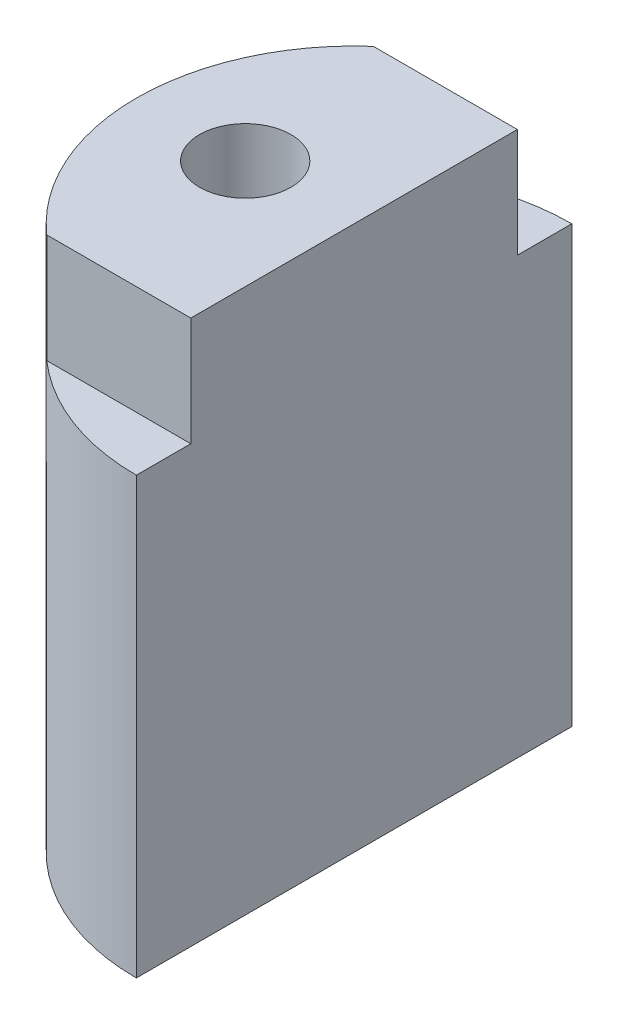
SolidWorks part; units mm, degrees
material "Brass"
ref_plane "Front Plane" through (0, 0, 0) normal (0, 0, 1) x (1, 0, 0)
ref_plane "Top Plane" through (0, 0, 0) normal (0, 1, 0) x (1, 0, 0)
ref_plane "Right Plane" through (0, 0, 0) normal (1, 0, 0) x (0, 0, -1)
sketch "Sketch1" plane through (0, 0, 0) normal (0, 1, 0) x (1, 0, 0)
  line L0 (0, 10) -> (0, -10)
  arc A4 (0, 10) -> (0, -10) centre (0, 0) ccw
  dimension "D1" = 20
extrude "Boss-Extrude1" add sketch "Sketch1" along normal blind 25
sketch "Sketch4" plane through (0, 25, 0) normal (0, 1, 0) x (1, 0, 0)
  circle A0 centre (0, 0) radius 3
  dimension "D1" = 6
sketch "Sketch18" plane through (0, 25, 0) normal (0, 1, 0) x (1, 0, 0)
  line L0 (0, 10) -> (0, -10)
  line L1 (0, 7.5) -> (-6.6144, 7.5)
  line L2 (0, -7.5) -> (-6.6144, -7.5)
  arc A1 (0, 10) -> (0, -10) centre (0, 0) ccw
  arc M6 (0, 10) -> (0, -10) centre (0, 0) ccw
  line M8 (0, -10) -> (0, 10)
  dimension "D1" = 7.5
  dimension "D2" = 20
  dimension "D3" = 7.5
extrude "Cut-Extrude1" cut sketch "Sketch18" against normal blind 5 contours L1 L0 M6 | L2 M8 M6
sketch "Sketch19" plane through (0, 25, 0) normal (0, 1, 0) x (1, 0, 0)
  line L0 (0, 0) -> (-10, 0) construction
  arc A0 (-6.6144, 7.5) -> (-6.6144, -7.5) centre (0, 0) ccw construction
hole_wizard "M5 Tapped Hole1" positions "Sketch20" profile "Sketch21" tap size "M5" standard "ISO"
sketch "Sketch20" plane through (0, 25, 0) normal (0, 1, 0) x (1, 0, 0)
  line L0 (0, 0) -> (-10, 0) construction
  point P0 (-5, 0)
sketch "Sketch21" plane through (-5, 25, 0) normal (1, 0, 0) x (0, 0, 1)
  line L0 (0, 0) -> (0, 12.4)
  line L1 (0, 12.4) -> (2.1, 11.1382)
  line L2 (2.1, 11.1382) -> (2.1, 0)
  line L5 (2.1, 0) -> (0, 0)
  line L10 (0, 12.4) -> (-2.1, 11.1382) construction
  line L11 (0, -6.35) -> (0, 107.95) construction
  dimension "Tap Drill Dia." = 4.2
  dimension "Tap Drill Depth" = 12.4
  dimension "Drill Angle" = 118
cosmetic thread "Hole Thread1" parameters "D1"=10, "D2"=5
